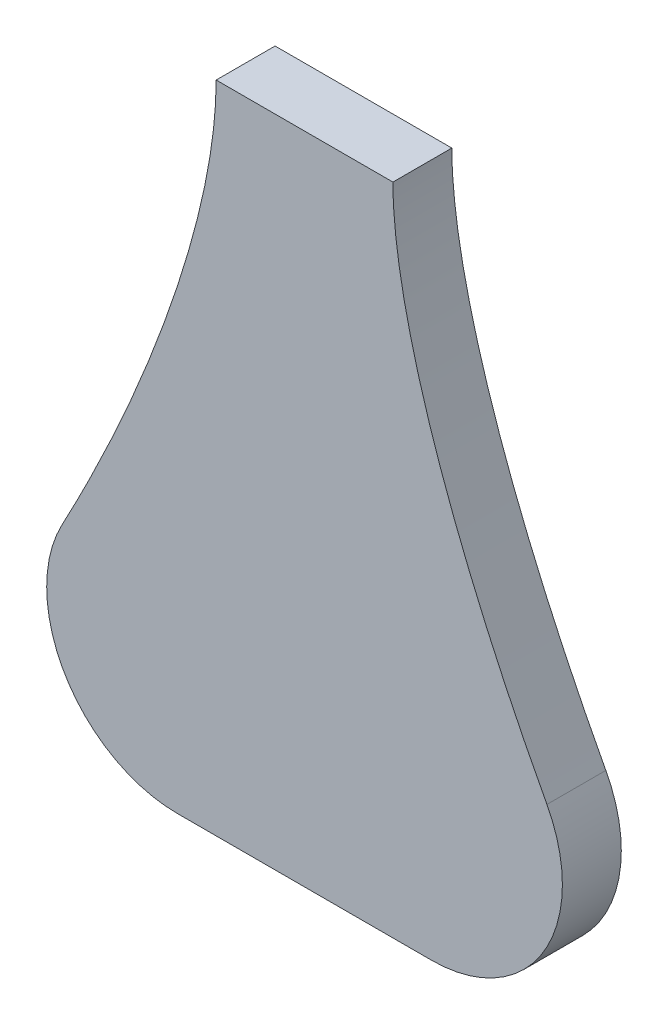
SolidWorks part; units mm, degrees
ref_plane "Спереди" through (0, 0, 0) normal (0, 0, 1) x (1, 0, 0)
ref_plane "Сверху" through (0, 0, 0) normal (0, 1, 0) x (1, 0, 0)
ref_plane "Справа" through (0, 0, 0) normal (1, 0, 0) x (0, 0, -1)
sketch "Sketch1" plane through (0, 0, 0) normal (0, 0, 1) x (1, 0, 0)
  line L0 (0, -3022.8419) -> (0, 148119.2507) construction
  line L1 (-27, 0) -> (27, 0)
  line L2 (27, -73.1635) -> (27, 73.1635) construction
  line L3 (110, -200) -> (-110, -200)
  spline S0 degree 3 poles (27, 0) (27, -49.0264) (64.5944, -134.9087) (110, -200) knots 0 0 0 0 1 1 1 1
  spline S1 degree 3 poles (-27, 0) (-27, -49.0264) (-64.5944, -134.9087) (-110, -200) knots 0 0 0 0 1 1 1 1
  point P10 (0, -200)
  point P11 (0, 0)
  dimension "D1" = 200
  dimension "D2" = 110
  dimension "D3" = 27
extrude "Boss-Extrude1" add sketch "Sketch1" along normal blind 18
fillet "Fillet1" radius 40 2 edges at (-110, -200, 9) (110, -200, 9)
